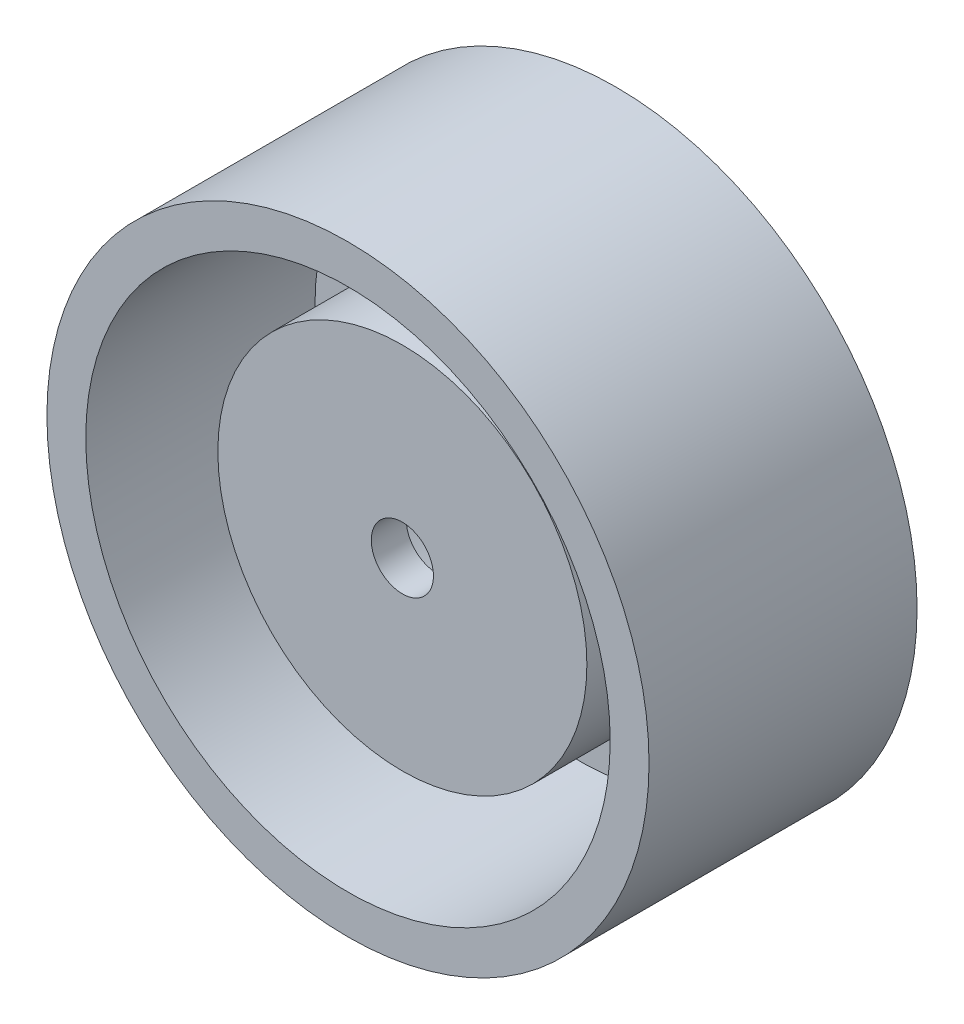
SolidWorks part; units mm, degrees
ref_plane "Front Plane" through (0, 0, 0) normal (0, 0, 1) x (1, 0, 0)
ref_plane "Top Plane" through (0, 0, 0) normal (0, 1, 0) x (1, 0, 0)
ref_plane "Right Plane" through (0, 0, 0) normal (1, 0, 0) x (0, 0, -1)
sketch "Sketch1" plane through (0, 0, 0) normal (0, 0, 1) x (1, 0, 0)
  circle A0 centre (-69.7695, 37.477) radius 19.685
  dimension "D1" = 39.37
extrude "Boss-Extrude4" add sketch "Sketch1" along normal blind 17.526
shell "Shell1" thickness 2.54
sketch "Sketch2" plane through (0, 0, 2.54) normal (0, 0, 1) x (1, 0, 0)
  circle A2 centre (-69.7695, 37.477) radius 12.065
extrude "Boss-Extrude5" add sketch "Sketch2" along normal blind 11.43
sketch "Sketch3" plane through (0, 0, 0) normal (0, 0, -1) x (-1, 0, 0)
  circle A1 centre (69.7695, 37.477) radius 10.795
  dimension "D1" = 21.59
extrude "Cut-Extrude1" cut sketch "Sketch3" against normal blind 11.684
sketch "Sketch4" plane through (0, 0, 13.97) normal (0, 0, 1) x (1, 0, 0)
  circle A0 centre (-69.7695, 37.477) radius 2.032
extrude "Cut-Extrude2" cut sketch "Sketch4" against normal blind 2.54
